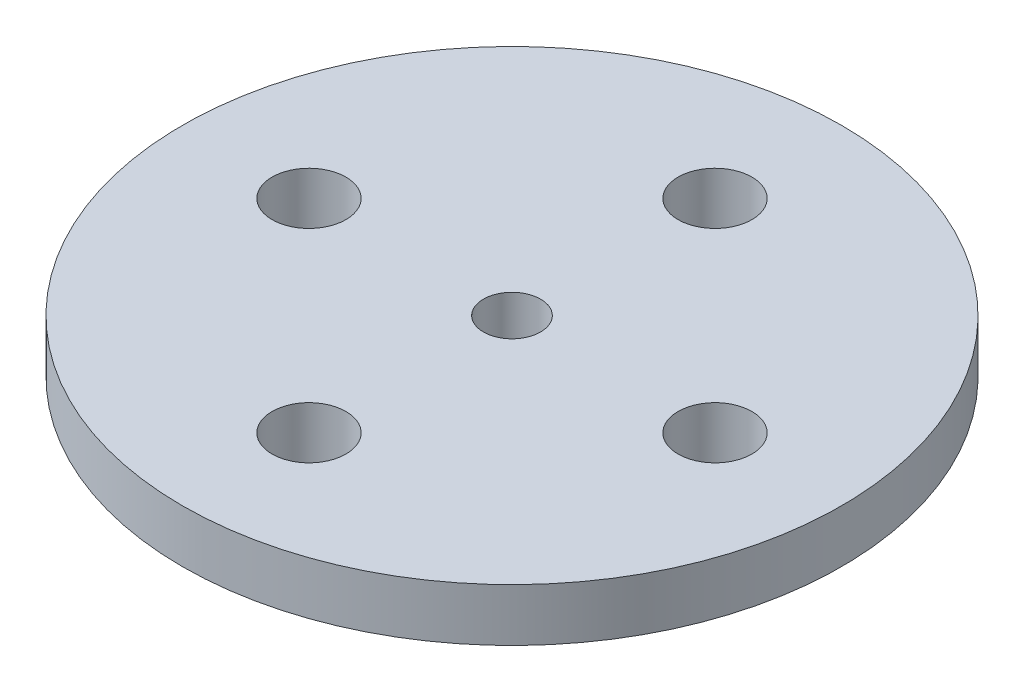
SolidWorks part; units mm, degrees
ref_plane "Front Plane" through (0, 0, 0) normal (0, 0, 1) x (1, 0, 0)
ref_plane "Top Plane" through (0, 0, 0) normal (0, 1, 0) x (1, 0, 0)
ref_plane "Right Plane" through (0, 0, 0) normal (1, 0, 0) x (0, 0, -1)
sketch "Sketch1" plane through (0, 0, 0) normal (0, 1, 0) x (1, 0, 0)
  line L0 (0, 15.5) -> (0, -15.5) construction
  line L1 (-15.5, 0) -> (15.5, 0) construction
  line L2 (-2.4674, 13.4022) -> (-4, 4) construction
  line L3 (4, -4) -> (-4, -4) construction
  line L4 (4, -4) -> (4, 4) construction
  line L5 (4, 4) -> (-4, 4) construction
  line L6 (-4, -4) -> (-4, 4) construction
  line L7 (4, -4) -> (-4, 4) construction
  line L8 (4, 4) -> (-4, -4) construction
  line L9 (-4, 4) -> (-2.4674, 13.4022)
  line L10 (4, 4) -> (2.4674, 13.4022)
  line L11 (4, -4) -> (2.4674, -13.4022)
  line L12 (-4, -4) -> (-2.4674, -13.4022)
  line L13 (-4, 4) -> (-12.5927, 2.4331) construction
  line L14 (-4, 4) -> (-12.4485, 2.4594)
  line L15 (-4, -4) -> (-12.4485, -2.4594)
  line L16 (4, -4) -> (12.4485, -2.4594)
  line L17 (4, 4) -> (12.4485, 2.4594)
  circle A0 centre (0, 0) radius 15.5 construction
  circle A1 centre (0, 0) radius 14.5 construction
  arc A2 (2.4674, 13.4022) -> (-2.4674, 13.4022) centre (0, 13) ccw
  arc A3 (2.4674, -13.4022) -> (-2.4674, -13.4022) centre (0, -13) cw
  arc A4 (-12.4485, 2.4594) -> (-12.4485, -2.4594) centre (-12, 0) ccw
  arc A5 (12.4485, 2.4594) -> (12.4485, -2.4594) centre (12, 0) cw
  circle A6 centre (0, 0) radius 12 construction
  circle A7 centre (0, 0) radius 9.5 construction
  circle A8 centre (0, 0) radius 7.5 construction
  circle A9 centre (0, 12) radius 0.5
  circle A10 centre (0, 9.5) radius 0.5
  circle A11 centre (0, 7.5) radius 0.5
  circle A12 centre (12, 0) radius 0.5
  circle A13 centre (9.5, 0) radius 0.5
  circle A14 centre (7.5, 0) radius 0.5
  circle A15 centre (0, -12) radius 0.5
  circle A16 centre (0, -9.5) radius 0.5
  circle A17 centre (0, -7.5) radius 0.5
  circle A18 centre (-12, 0) radius 0.5
  circle A19 centre (-9.5, 0) radius 0.5
  circle A20 centre (-7.5, 0) radius 0.5
  circle A21 centre (0, 0) radius 1.375
  point P59 (0, 0)
  dimension "D1" = 31
  dimension "D2" = 1
  dimension "D3" = 5
  dimension "D4" = 5
  dimension "D5" = 8
  dimension "D6" = 8
  dimension "D7" = 15
  dimension "D9" = 24
  dimension "D11" = 1
  dimension "D12" = 1
  dimension "D13" = 4
  dimension "D8" = 19
  dimension "D10" = 1
  dimension "D14" = 2.75
extrude "Boss-Extrude1" add sketch "Sketch1" along normal blind 2
sketch "Sketch4" plane through (0, 0, 0) normal (0, -1, 0) x (1, 0, 0)
  circle A0 centre (0, 0) radius 4.627
  circle A1 centre (0, 0) radius 2.627
  dimension "D1" = 9.254
  dimension "D2" = 2
extrude "Boss-Extrude3" add sketch "Sketch4" along normal blind 2.5
sketch "Sketch5" plane through (0, -2.5, 0) normal (0, -1, 0) x (1, 0, 0)
  line L0 (0, 0) -> (0, 0.6245) construction
  line L1 (0, 3.1016) -> (-0.2828, 2.6117)
  line L2 (0, 3.1016) -> (0.2828, 2.6117)
  line L3 (0.9584, 2.9498) -> (0.5381, 2.5713)
  line L4 (0.9584, 2.9498) -> (1.076, 2.3965)
  line L5 (1.8231, 2.5092) -> (1.3063, 2.2792)
  line L6 (1.8231, 2.5092) -> (1.7639, 1.9467)
  line L7 (2.5092, 1.8231) -> (1.9467, 1.7639)
  line L8 (2.5092, 1.8231) -> (2.2792, 1.3063)
  line L9 (2.9498, 0.9584) -> (2.3965, 1.076)
  line L10 (2.9498, 0.9584) -> (2.5713, 0.5381)
  line L11 (3.1016, 0) -> (2.6117, 0.2828)
  line L12 (3.1016, 0) -> (2.6117, -0.2828)
  line L13 (2.9498, -0.9584) -> (2.5713, -0.5381)
  line L14 (2.9498, -0.9584) -> (2.3965, -1.076)
  line L15 (2.5092, -1.8231) -> (2.2792, -1.3063)
  line L16 (2.5092, -1.8231) -> (1.9467, -1.7639)
  line L17 (1.8231, -2.5092) -> (1.7639, -1.9467)
  line L18 (1.8231, -2.5092) -> (1.3063, -2.2792)
  line L19 (0.9584, -2.9498) -> (1.076, -2.3965)
  line L20 (0.9584, -2.9498) -> (0.5381, -2.5713)
  line L21 (0, -3.1016) -> (0.2828, -2.6117)
  line L22 (0, -3.1016) -> (-0.2828, -2.6117)
  line L23 (-0.9584, -2.9498) -> (-0.5381, -2.5713)
  line L24 (-0.9584, -2.9498) -> (-1.076, -2.3965)
  line L25 (-1.8231, -2.5092) -> (-1.3063, -2.2792)
  line L26 (-1.8231, -2.5092) -> (-1.7639, -1.9467)
  line L27 (-2.5092, -1.8231) -> (-1.9467, -1.7639)
  line L28 (-2.5092, -1.8231) -> (-2.2792, -1.3063)
  line L29 (-2.9498, -0.9584) -> (-2.3965, -1.076)
  line L30 (-2.9498, -0.9584) -> (-2.5713, -0.5381)
  line L31 (-3.1016, 0) -> (-2.6117, -0.2828)
  line L32 (-3.1016, 0) -> (-2.6117, 0.2828)
  line L33 (-2.9498, 0.9584) -> (-2.5713, 0.5381)
  line L34 (-2.9498, 0.9584) -> (-2.3965, 1.076)
  line L35 (-2.5092, 1.8231) -> (-2.2792, 1.3063)
  line L36 (-2.5092, 1.8231) -> (-1.9467, 1.7639)
  line L37 (-1.8231, 2.5092) -> (-1.7639, 1.9467)
  line L38 (-1.8231, 2.5092) -> (-1.3063, 2.2792)
  line L39 (-0.9584, 2.9498) -> (-1.076, 2.3965)
  line L40 (-0.9584, 2.9498) -> (-0.5381, 2.5713)
  circle A0 centre (0, 0) radius 2.627 construction
  arc A1 (-2.2792, 1.3063) -> (-2.3965, 1.076) centre (0, 0) ccw
  arc A2 (-1.7639, 1.9467) -> (-1.9467, 1.7639) centre (0, 0) ccw
  arc A3 (-1.076, 2.3965) -> (-1.3063, 2.2792) centre (0, 0) ccw
  arc A4 (-0.2828, 2.6117) -> (-0.5381, 2.5713) centre (0, 0) ccw
  arc A5 (0.5381, 2.5713) -> (0.2828, 2.6117) centre (0, 0) ccw
  arc A6 (1.3063, 2.2792) -> (1.076, 2.3965) centre (0, 0) ccw
  arc A7 (1.9467, 1.7639) -> (1.7639, 1.9467) centre (0, 0) ccw
  arc A8 (2.3965, 1.076) -> (2.2792, 1.3063) centre (0, 0) ccw
  arc A9 (2.6117, 0.2828) -> (2.5713, 0.5381) centre (0, 0) ccw
  arc A10 (2.5713, -0.5381) -> (2.6117, -0.2828) centre (0, 0) ccw
  arc A11 (2.2792, -1.3063) -> (2.3965, -1.076) centre (0, 0) ccw
  arc A12 (1.7639, -1.9467) -> (1.9467, -1.7639) centre (0, 0) ccw
  arc A13 (1.076, -2.3965) -> (1.3063, -2.2792) centre (0, 0) ccw
  arc A14 (0.2828, -2.6117) -> (0.5381, -2.5713) centre (0, 0) ccw
  arc A15 (-0.5381, -2.5713) -> (0, -2.627) centre (0, 0) ccw
  arc A16 (-1.3063, -2.2792) -> (-1.076, -2.3965) centre (0, 0) ccw
  arc A17 (-1.9467, -1.7639) -> (-1.7639, -1.9467) centre (0, 0) ccw
  arc A18 (-2.3965, -1.076) -> (-2.2792, -1.3063) centre (0, 0) ccw
  arc A19 (-2.6117, -0.2828) -> (-2.5713, -0.5381) centre (0, 0) ccw
  arc A20 (-2.5713, 0.5381) -> (-2.6117, 0.2828) centre (0, 0) ccw
  point P68 (0, 0)
  circle M5 centre (0, 0) radius 2.627
  dimension "D1" = 30
  dimension "D2" = 3.1016
  dimension "D3" = 20
extrude "Cut-Extrude3" cut sketch "Sketch5" against normal up to surface (2.5 mm away) contours L36 L35 M5 | L34 L33 M5 | L32 L31 M5 | L30 L29 M5 | L28 L27 M5 | L26 L25 M5 | L24 L23 M5 | L0 L21 M5 | L22 L0 M5 | L20 L19 M5 | L18 L17 M5 | L16 L15 M5 | L14 L13 M5 | L12 L11 M5 | L10 L9 M5 | L8 L7 M5 | L6 L5 M5 | L4 L3 M5 | L0 L2 M5 | L0 L1 M5 | L40 L39 M5 | L38 L37 M5
sketch "Sketch6" plane through (0, 2, 0) normal (0, 1, 0) x (1, 0, 0)
  circle A0 centre (0, 0) radius 15.875
  circle A2 centre (0, 0) radius 3.75
  dimension "D1" = 31.75
extrude "Boss-Extrude6" add sketch "Sketch6" against normal blind 2.54
sketch "Sketch7" plane through (0, 2, 0) normal (0, 1, 0) x (1, 0, 0)
  circle A0 centre (0, 9.779) radius 1.778
extrude "Cut-Extrude4" cut sketch "Sketch7" against normal blind 2.54
pattern_circular "CirPattern1" count 4 over 360 about axis through (0, 0, 0) along (0, 1, 0) of "Cut-Extrude4"
